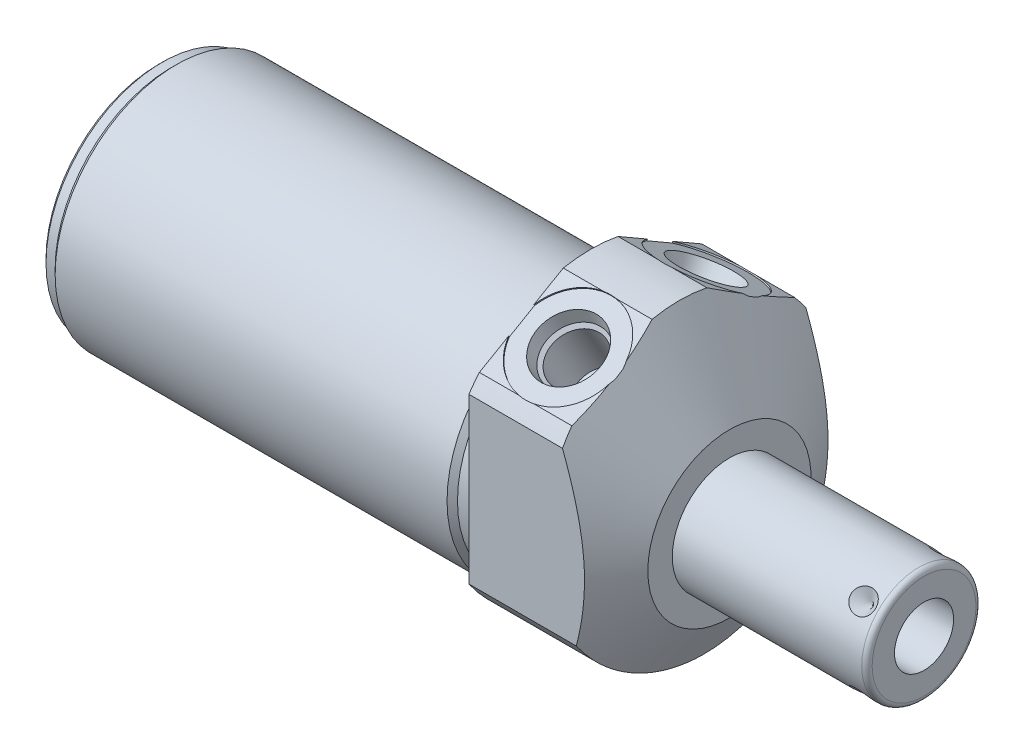
SolidWorks part; units mm, degrees
material "Alloy Steel"
ref_plane "Front Plane" through (0, 0, 0) normal (0, 0, 1) x (1, 0, 0)
ref_plane "Top Plane" through (0, 0, 0) normal (0, 1, 0) x (1, 0, 0)
ref_plane "Right Plane" through (0, 0, 0) normal (1, 0, 0) x (0, 0, -1)
ref_plane "Plane1" through (0, 0, 0) normal (1, 0, 0) x (0, 0, -1)
sketch "Sketch1" plane through (0, 0, 0) normal (1, 0, 0) x (0, 0, -1)
  circle A0 centre (0, 0) radius 28.575
  dimension "D1" = 57.15
extrude "Extrude1" add sketch "Sketch1" along normal blind 27.0002 and the other way blind 84.1248
ref_plane "Plane2" through (0, 0, 0) normal (1, 0, 0) x (0, 0, -1)
sketch "Sketch2" plane through (0, 0, 0) normal (1, 0, 0) x (0, 0, -1)
  line L0 (-25.9842, -4.191) -> (25.9842, -4.191) construction
  circle A0 centre (0, -4.191) radius 23.622
  circle A2 centre (0, 0) radius 28.575
  circle A3 centre (0, 0) radius 28.575
  dimension "D2" = 47.244
  dimension "D1" = 4.191
  dimension "D3" = 0
extrude "Cut-Extrude1" cut sketch "Sketch2" against normal up to next
ref_plane "Plane4" through (0, 0, 0) normal (-1, 0, 0) x (0, 0, 1)
sketch "Sketch4" plane through (0, 0, 0) normal (-1, 0, 0) x (0, 0, 1)
  line L0 (23.6855, -25.6662) -> (23.6855, 17.4761)
  line L1 (23.6855, 17.4761) -> (0, 31.1509)
  line L2 (-23.6855, -25.6662) -> (-23.6855, 17.4761)
  line L3 (-23.6855, 17.4761) -> (0, 31.1509)
  line L4 (0, -31.5613) -> (0, 34.1372) construction
  arc A2 (23.6855, -25.6662) -> (-23.6855, -25.6662) centre (0, 0) ccw
  dimension "D4" = 69.85
  dimension "D1" = 47.371
  dimension "D2" = 30.607
  dimension "D3" = 120
extrude "Cut-Extrude3" cut sketch "Sketch4" against normal up to next
ref_plane "Plane6" through (0, 0, 0) normal (0, 0, 1) x (1, 0, 0)
sketch "Sketch6" plane through (0, 0, 0) normal (0, 0, 1) x (1, 0, 0)
  line L0 (0.7504, 57.15) -> (27.0002, 11.684)
  line L1 (-0.5621, -4.191) -> (28.3127, -4.191) construction
  line L2 (-84.1248, -4.191) -> (0, -4.191) construction
  line L3 (27.0002, 11.684) -> (27.0002, 57.15)
  line L4 (27.0002, 57.15) -> (0.7504, 57.15)
  line L5 (27.0002, 15.9852) -> (27.0002, -15.9852) construction
  dimension "D1" = 60
  dimension "D2" = 31.75
  dimension "D3" = 122.682
revolve "Cut-Revolve2" cut sketch "Sketch6" angle 360 about L1
ref_plane "Plane7" through (9.0932, 23.1369, 13.3727) normal (1, 0, 0) x (0, 0.5, -0.866)
sketch "S2D0002" plane through (9.0932, 23.1369, 13.3727) normal (1, 0, 0) x (0, 0.5, -0.866)
  line L0 (0, 0) -> (6.1849, 0)
  line L1 (6.1849, 0) -> (5.6423, -2.5527)
  line L2 (5.6423, -2.5527) -> (4.9784, -3.2166)
  line L3 (4.9784, -3.2166) -> (4.9784, -13.462)
  line L4 (4.9784, -13.462) -> (0, -13.462)
  line L5 (0, -13.462) -> (0, 0)
  line L6 (0, -14.1351) -> (0, 0.6731) construction
  dimension "D1" = 13.462
revolve "Cut-Revolve3" cut sketch "S2D0002" angle 360 about L6
ref_plane "Plane8" through (9.0932, 23.1369, -13.3727) normal (1, 0, 0) x (0, -0.5, -0.866)
sketch "Sketch8" plane through (9.0932, 23.1369, -13.3727) normal (1, 0, 0) x (0, -0.5, -0.866)
  line L0 (0, 0) -> (6.1849, 0)
  line L1 (6.1849, 0) -> (5.6423, -2.5527)
  line L2 (5.6423, -2.5527) -> (4.9784, -3.2166)
  line L3 (4.9784, -3.2166) -> (4.9784, -13.462)
  line L4 (4.9784, -13.462) -> (0, -13.462)
  line L5 (0, -13.462) -> (0, 0)
  line L6 (0, -14.1351) -> (0, 0.6731) construction
  dimension "D1" = 13.462
revolve "Cut-Revolve4" cut sketch "Sketch8" angle 360 about L6
ref_plane "Plane10" through (0, 0, 0) normal (0, 0, 1) x (1, 0, 0)
sketch "Sketch18" plane through (0, 23.3632, 13.4887) normal (0, 0.866, 0.5) x (1, 0, 0)
  circle A0 centre (9.0932, -0.0127) radius 9.525
  dimension "D1" = 19.05
extrude "Cut-Extrude4" cut sketch "Sketch18" against normal blind 0.254
sketch "Sketch19" plane through (0, 23.3632, -13.4887) normal (0, 0.866, -0.5) x (1, 0, 0)
  circle A0 centre (9.0932, 0.0127) radius 9.525
  circle A1 centre (9.0932, 0.0127) radius 6.1849 construction
  dimension "D1" = 19.05
extrude "Cut-Extrude5" cut sketch "Sketch19" against normal blind 0.254
sketch "Sketch10" plane through (0, 0, 0) normal (0, 0, 1) x (1, 0, 0)
  line L0 (0, 19.431) -> (0, 18.415)
  line L1 (0, 18.415) -> (-3.302, 18.415)
  line L2 (-3.302, 18.415) -> (-4.318, 19.431)
  line L3 (-4.5339, -4.191) -> (0.2159, -4.191) construction
  line L4 (0, 19.431) -> (-4.318, 19.431)
  line L5 (-84.1248, -4.191) -> (0, -4.191) construction
  line L6 (0, 19.431) -> (-84.1248, 19.431) construction
  line L7 (0, 21.9392) -> (0, 18.6529) construction
  dimension "D1" = 45.212
  dimension "D2" = 45
  dimension "D3" = 3.302
revolve "Cut-Revolve6" cut sketch "Sketch10" angle 360 about L3
ref_plane "Plane12" through (0, 0, 0) normal (0, 0, 1) x (1, 0, 0)
sketch "Sketch12" plane through (0, 0, 0) normal (0, 0, 1) x (1, 0, 0)
  line L0 (-84.1248, 19.431) -> (-84.1248, 18.415)
  line L1 (-84.1248, 18.415) -> (-81.5848, 18.415)
  line L2 (-81.5848, 18.415) -> (-80.5688, 19.431)
  line L3 (-84.3026, -4.191) -> (-80.391, -4.191) construction
  line L4 (-84.1248, 19.431) -> (-80.5688, 19.431)
  line L5 (-84.1248, -4.191) -> (-4.318, -4.191) construction
  line L6 (-4.318, 19.431) -> (-84.1248, 19.431) construction
  line L7 (-84.1248, 19.431) -> (-84.1248, -27.813) construction
  dimension "D1" = 45.212
  dimension "D2" = 45
  dimension "D3" = 2.54
revolve "Cut-Revolve8" cut sketch "Sketch12" angle 360 about L3
chamfer "Chamfer1" distance 0.762 angle 45 1 edges at (-84.1248, -4.191, 22.606)
ref_plane "Plane13" through (0, 0, 0) normal (0, 0, 1) x (0, -1, 0)
sketch "Sketch13" plane through (0, 0, 0) normal (0, 0, 1) x (0, -1, 0)
  line L0 (4.191, 27.0002) -> (4.191, 64.8716)
  line L1 (4.191, 64.8716) -> (14.2875, 64.8716)
  line L2 (15.3035, 63.8556) -> (15.3035, 27.0002)
  line L3 (15.3035, 27.0002) -> (4.191, 27.0002)
  line L4 (4.191, 25.1066) -> (4.191, 66.7652) construction
  line L5 (4.191, -80.5688) -> (4.191, -4.318) construction
  line L6 (20.066, 27.0002) -> (-11.684, 27.0002) construction
  line L7 (-18.415, 0) -> (26.797, 0) construction
  arc A0 (15.3035, 63.8556) -> (14.2875, 64.8716) centre (14.2875, 63.8556) ccw
  dimension "D3" = 1.016
  dimension "D1" = 22.225
  dimension "D2" = 64.8716
revolve "Revolve1" add sketch "Sketch13" angle 360 about L4
ref_plane "Plane14" through (64.8716, -9.9441, 0) normal (0, 0, 1) x (0, -1, 0)
sketch "S2D0001" plane through (64.8716, -9.9441, 0) normal (0, 0, 1) x (0, -1, 0)
  line L0 (0, 0) -> (0, -17.018)
  line L1 (0, -17.018) -> (-5.7531, -20.4748)
  line L2 (0, 0) -> (-5.7531, 0)
  line L3 (-5.7531, 0) -> (-5.7531, -20.4748)
  line L4 (-5.7531, -21.4986) -> (-5.7531, 1.0237) construction
  line L5 (-5.7531, -1.016) -> (-5.7531, -37.8714) construction
  line L6 (4.3434, 0) -> (-15.8496, 0) construction
  dimension "D1" = 11.5062
  dimension "D2" = 59
  dimension "D3" = 17.018
revolve "Cut-Revolve9" cut sketch "S2D0001" angle 360 about L4
ref_plane "Plane16" through (60.9092, -15.3035, 0) normal (0, 0, 1) x (-1, 0, 0)
ref_plane "Plane17" through (0, -2.0955, -2.0955) normal (0, 0.7071, 0.7071) x (-1, 0, 0)
sketch "Sketch16" plane through (60.9092, 3.6667, -7.8577) normal (0, -0.7071, -0.7071) x (-1, 0, 0)
  line L0 (0, 0) -> (2.413, 0)
  line L1 (2.413, 0) -> (0, -2.413)
  line L2 (0, 0) -> (0, -2.413)
  line L3 (0, -4.4865) -> (0, 0.1207) construction
  line L4 (-3.9624, -1.016) -> (-3.9624, -21.209) construction
  line L5 (33.909, 0) -> (-2.9464, 0) construction
  dimension "D1" = 45
  dimension "D2" = 3.9624
  dimension "D3" = 4.826
revolve "Cut-Revolve10" cut sketch "Sketch16" angle 360 about L3
pattern_circular "CirPattern1" count 4 over 360 about axis through (25.1066, -4.191, 0) along (-1, 0, 0) of "Cut-Revolve10"
